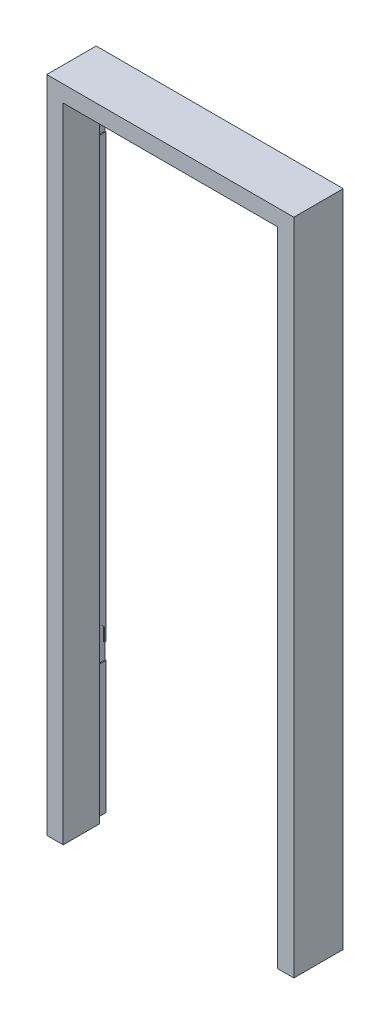
SolidWorks part; units mm, degrees
material "Mahogany"
ref_plane "Front Plane" through (0, 0, 0) normal (0, 0, 1) x (1, 0, 0)
ref_plane "Top Plane" through (0, 0, 0) normal (0, 1, 0) x (1, 0, 0)
ref_plane "Right Plane" through (0, 0, 0) normal (1, 0, 0) x (0, 0, -1)
sketch "Sketch1" plane through (0, 0, 0) normal (0, 0, 1) x (1, 0, 0)
  line L1 (0, 0) -> (-750, 0)
  line L2 (0, 0) -> (0, -2000)
  line L4 (-750, 0) -> (-750, -2000)
  line L9 (-750, -2000) -> (-700, -2000)
  line L10 (-50, -2000) -> (0, -2000)
  line L12 (-50, -2000) -> (-50, -50)
  line L13 (-50, -50) -> (-700, -50)
  line L14 (-700, -2000) -> (-700, -50)
  dimension "D1" = 2000
  dimension "D2" = 750
  dimension "D3" = 50
  dimension "D4" = 50
  dimension "D5" = 50
extrude "Boss-Extrude1" add sketch "Sketch1" along normal blind 150
sketch "Sketch4" plane through (0, 0, 0) normal (0, 0, -1) x (-1, 0, 0)
  line L0 (750, 0) -> (750, -2000) construction
  line L1 (30, -30) -> (720, -30)
  line L2 (30, -30) -> (30, -2000)
  line L3 (30, -2000) -> (720, -2000)
  line L4 (720, -30) -> (720, -2000)
  line L5 (0, -2000) -> (0, 0) construction
  line L6 (0, 0) -> (750, 0) construction
  dimension "D1" = 30
  dimension "D2" = 30
  dimension "D3" = 30
extrude "Cut-Extrude1" cut sketch "Sketch4" against normal blind 40
sketch "Sketch5" plane through (-30, 0, 0) normal (-1, 0, 0) x (0, 0, 1)
  line L0 (40, -30) -> (40, -2000) construction
  line L1 (5, -960) -> (35, -960)
  line L2 (5, -960) -> (5, -1130)
  line L3 (5, -1130) -> (35, -1130)
  line L4 (35, -960) -> (35, -1130)
  line L5 (0, -30) -> (0, -2000) construction
  line L6 (40, -30) -> (0, -30) construction
  dimension "D1" = 5
  dimension "D2" = 5
  dimension "D3" = 930
  dimension "D4" = 170
extrude "Cut-Extrude2" cut sketch "Sketch5" against normal blind 5
sketch "Sketch6" plane through (-720, 0, 0) normal (1, 0, 0) x (0, 0, -1)
  line L0 (-35, -120) -> (-35, -210)
  line L2 (-5, -120) -> (-5, -160)
  line L3 (-5, -160) -> (0, -160)
  line L4 (0, -2000) -> (0, -30) construction
  line L5 (0, -160) -> (0, -210)
  line L6 (0, -210) -> (-35, -210)
  line L7 (-40, -2000) -> (0, -2000) construction
  line L8 (-40, -2000) -> (-40, -30) construction
  line L9 (-35, -1510) -> (-35, -1600)
  line L11 (-5, -1510) -> (-5, -1550)
  line L12 (-5, -1550) -> (0, -1550)
  line L13 (0, -1550) -> (0, -1600)
  line L14 (0, -1600) -> (-35, -1600)
  arc A0 (-35, -120) -> (-5, -120) centre (-20, -126.25) cw
  arc A1 (-35, -1510) -> (-5, -1510) centre (-20, -1516.25) cw
  point P0 (-35, -1510)
  point P2 (-5, -1510)
  dimension "D2" = 400
  dimension "D4" = 5
  dimension "D5" = 5
  dimension "D9" = 5
  dimension "D12" = 5
extrude "Cut-Extrude3" cut sketch "Sketch6" against normal blind 3
